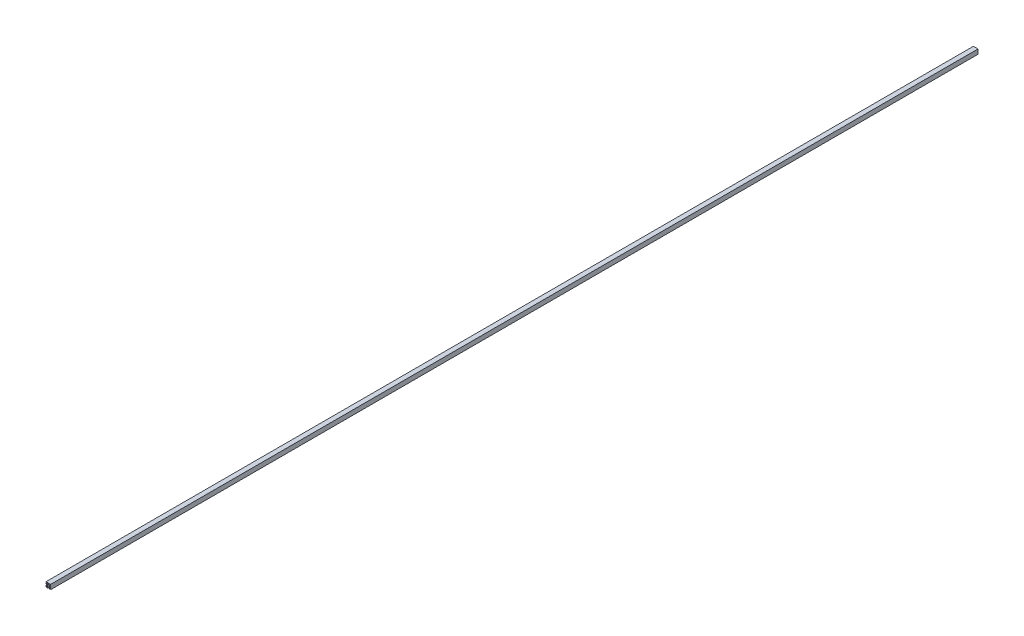
SolidWorks part; units mm, degrees
ref_plane "Front Plane" through (0, 0, 0) normal (0, 0, 1) x (1, 0, 0)
ref_plane "Top Plane" through (0, 0, 0) normal (0, 1, 0) x (1, 0, 0)
ref_plane "Right Plane" through (0, 0, 0) normal (1, 0, 0) x (0, 0, -1)
sketch "Sketch1" plane through (0, 0, 0) normal (0, 0, 1) x (1, 0, 0)
  line L64 (10.5786, -8.5) -> (9.3444, -8.5)
  line L65 (-8.5, 9.3444) -> (-8.5, 10.5786)
  line L66 (-2.6003, 7.55) -> (-3.4265, 8.3762)
  line L67 (3.4265, 8.3762) -> (2.6003, 7.55)
  line L68 (7.55, 2.6003) -> (8.3762, 3.4265)
  line L69 (8.3762, -3.4265) -> (7.55, -2.6003)
  line L70 (15, -15) -> (13.5, -15)
  line L71 (12.7, -7.5) -> (13.5, -7.5)
  line L72 (10.3, -10) -> (11.5342, -10)
  line L73 (7.2657, -11.6343) -> (7.2657, -13)
  line L74 (-7.2657, -13) -> (-7.2657, -11.6343)
  line L75 (-11.6343, -7.2657) -> (-13, -7.2657)
  line L76 (-13, 7.2657) -> (-11.6343, 7.2657)
  line L77 (-10, 11.5342) -> (-10, 10.3)
  line L78 (-7.5, 13.5) -> (-7.5, 12.7)
  line L79 (-15, 13.5) -> (-15, 15)
  line L80 (-13.5, -13.5) -> (-13.5, -9)
  line L81 (-13.5, -9) -> (-9, -9)
  line L82 (-9, -9) -> (-9, -13.5)
  line L83 (-9, -13.5) -> (-13.5, -13.5)
  line L84 (-7.4235, 5.1762) -> (-10.6085, 8.3612)
  line L85 (-10.6085, 8.3612) -> (-8.5, 9.3444)
  line L86 (-8.5, 10.5786) -> (-6, 11.7444)
  line L87 (-6, 11.7444) -> (-6, 13.5)
  line L88 (-6, 13.5) -> (13.5, 13.5)
  line L89 (13.5, 13.5) -> (13.5, -6)
  line L90 (13.5, -6) -> (11.7444, -6)
  line L91 (11.7444, -6) -> (10.5786, -8.5)
  line L92 (9.3444, -8.5) -> (8.3612, -10.6085)
  line L93 (8.3612, -10.6085) -> (5.1762, -7.4235)
  line L94 (5.1762, -7.4235) -> (8.3762, -3.4265)
  line L95 (7.55, -2.6003) -> (7.55, 2.6003)
  line L96 (8.3762, 3.4265) -> (6.1755, 6.1755)
  line L97 (6.1755, 6.1755) -> (3.4265, 8.3762)
  line L98 (2.6003, 7.55) -> (-2.6003, 7.55)
  line L99 (-3.4265, 8.3762) -> (-7.4235, 5.1762)
  line L100 (-15, -4) -> (-15, -15)
  line L101 (-15, -15) -> (-4, -15)
  line L102 (-4, -15) -> (-4, -13)
  line L103 (-4, -13) -> (-7.2657, -13)
  line L104 (-7.2657, -11.6343) -> (-3.9314, -8.3)
  line L105 (-3.9314, -8.3) -> (3.9314, -8.3)
  line L106 (3.9314, -8.3) -> (7.2657, -11.6343)
  line L107 (7.2657, -13) -> (4, -13)
  line L108 (4, -13) -> (4, -15)
  line L109 (4, -15) -> (9.4, -15)
  line L110 (9.4, -15) -> (9.4, -11.9301)
  line L111 (9.4, -11.9301) -> (10.3, -10)
  line L112 (11.5342, -10) -> (12.7, -7.5)
  line L113 (13.5, -7.5) -> (13.5, -15)
  line L114 (15, -15) -> (15, 15)
  line L115 (15, 15) -> (-15, 15)
  line L116 (-15, 13.5) -> (-7.5, 13.5)
  line L117 (-7.5, 12.7) -> (-10, 11.5342)
  line L118 (-10, 10.3) -> (-11.9301, 9.4)
  line L119 (-11.9301, 9.4) -> (-15, 9.4)
  line L120 (-15, 9.4) -> (-15, 4)
  line L121 (-15, 4) -> (-13, 4)
  line L122 (-13, 4) -> (-13, 7.2657)
  line L123 (-11.6343, 7.2657) -> (-8.3, 3.9314)
  line L124 (-8.3, 3.9314) -> (-8.3, -3.9314)
  line L125 (-8.3, -3.9314) -> (-11.6343, -7.2657)
  line L126 (-13, -7.2657) -> (-13, -4)
  line L127 (-13, -4) -> (-15, -4)
  circle A1 centre (0, 0) radius 6.05
extrude "Extrude1" add sketch "Sketch1" against normal blind 6000
sketch "Sketch2" plane through (0, 0, 0) normal (0, 0, 1) x (1, 0, 0)
  line L0 (-11.25, -9) -> (-7.7748, -5.5269)
  line L1 (-9, -9) -> (-13.5, -9) construction
  line L2 (-9, -11.25) -> (-5.5248, -7.7769)
  line L3 (-9, -13.5) -> (-9, -9) construction
  line L4 (-5.5248, -7.7769) -> (-7.7748, -5.5269)
  line L5 (-11.25, -9) -> (-9, -11.25)
extrude "Cut-Extrude1" cut sketch "Sketch2" against normal through all
